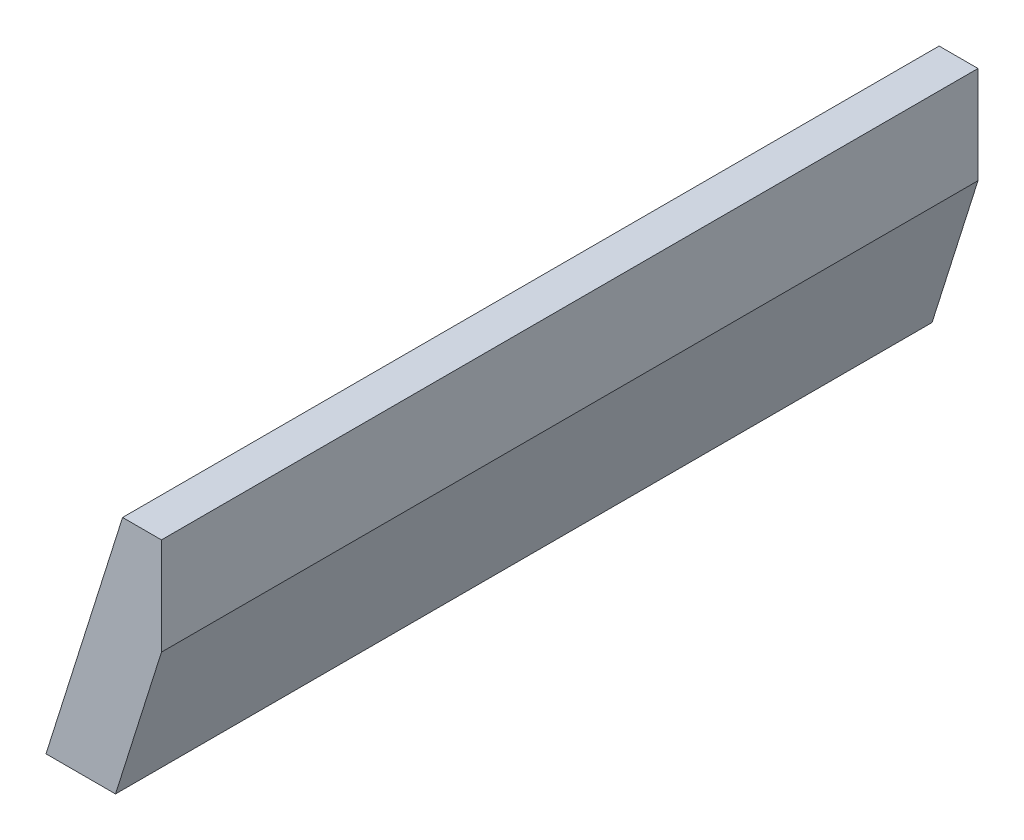
SolidWorks part; units mm, degrees
ref_plane "Front Plane" through (0, 0, 0) normal (0, 0, 1) x (1, 0, 0)
ref_plane "Top Plane" through (0, 0, 0) normal (0, 1, 0) x (1, 0, 0)
ref_plane "Right Plane" through (0, 0, 0) normal (1, 0, 0) x (0, 0, -1)
sketch "Sketch1" plane through (0, 0, 0) normal (0, 0, 1) x (1, 0, 0)
  line L12 (5.4446, 11.9495) -> (5.4446, 1.9495)
  line L13 (5.4446, 1.9495) -> (0.718, -13.0505)
  line L18 (5.4446, 11.9495) -> (1.4446, 11.9495)
  line L19 (1.4446, 11.9495) -> (-6.4331, -13.0505)
  line L20 (-6.4331, -13.0505) -> (0.718, -13.0505)
  dimension "D1" = 10
  dimension "D2" = 15
  dimension "D3" = 197.49
  dimension "D4" = 4
extrude "Boss-Extrude1" add sketch "Sketch1" along normal mid plane 84
